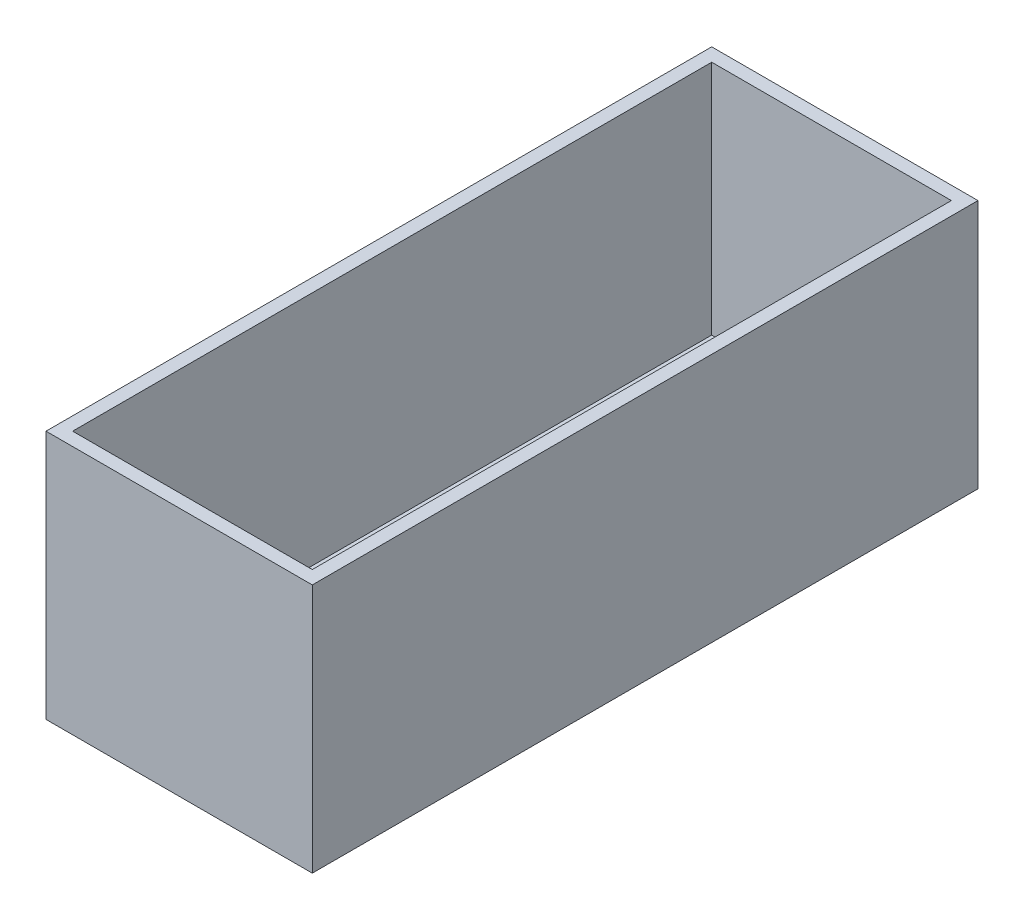
SolidWorks part; units mm, degrees
ref_plane "Front Plane" through (0, 0, 0) normal (0, 0, 1) x (1, 0, 0)
ref_plane "Top Plane" through (0, 0, 0) normal (0, 1, 0) x (1, 0, 0)
ref_plane "Right Plane" through (0, 0, 0) normal (1, 0, 0) x (0, 0, -1)
sketch "Sketch1" plane through (0, 0, 0) normal (0, 0, 1) x (1, 0, 0)
  line L1 (0, 0) -> (80, 0)
  line L2 (0, 0) -> (0, 75)
  line L3 (0, 75) -> (80, 75)
  line L4 (80, 0) -> (80, 75)
  dimension "D1" = 80
  dimension "D2" = 75
extrude "Boss-Extrude1" add sketch "Sketch1" against normal blind 200
shell "Shell1" thickness 4
